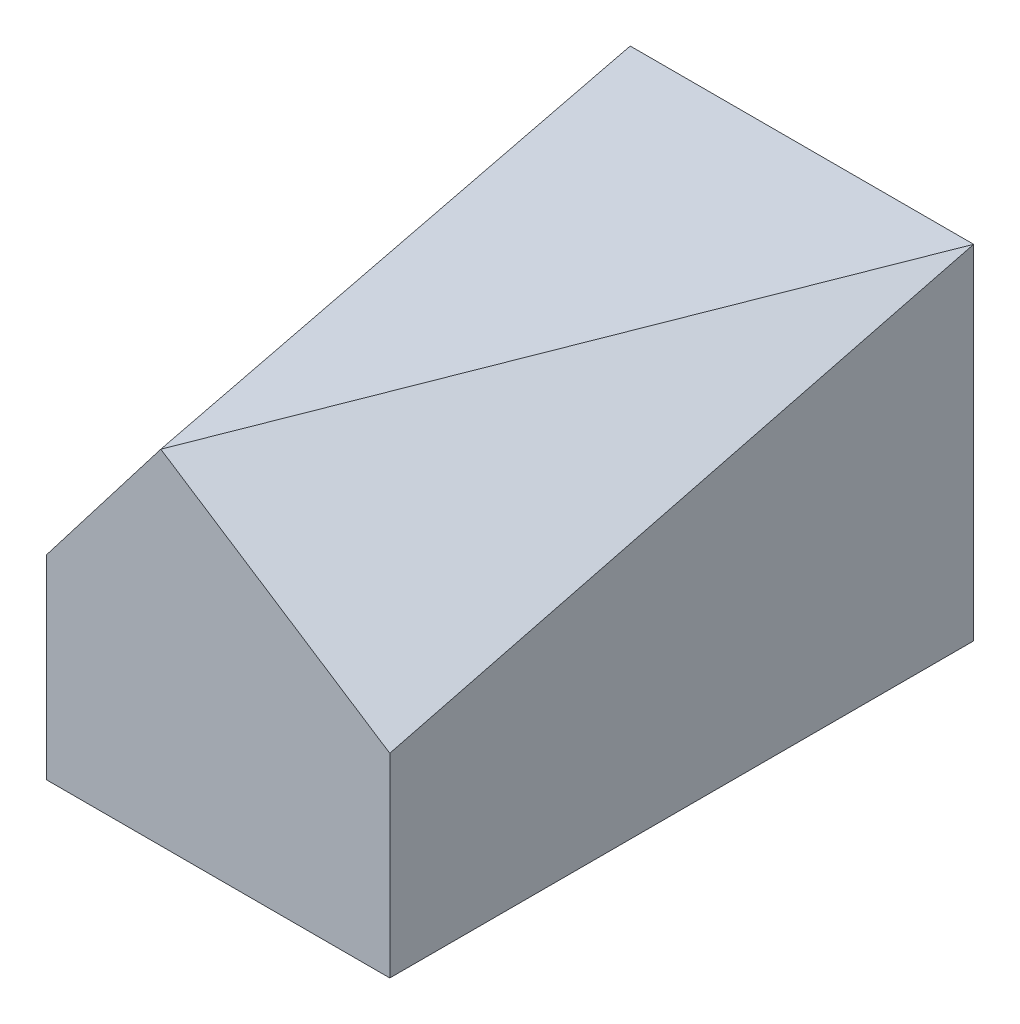
SolidWorks part; units mm, degrees
ref_plane "Front Plane" through (0, 0, 0) normal (0, 0, 1) x (1, 0, 0)
ref_plane "Top Plane" through (0, 0, 0) normal (0, 1, 0) x (1, 0, 0)
ref_plane "Right Plane" through (0, 0, 0) normal (1, 0, 0) x (0, 0, -1)
sketch "Sketch2" plane through (0, 0, 0) normal (0, 1, 0) x (1, 0, 0)
  line L0 (0, 0) -> (0, 51)
  line L1 (0, 51) -> (30, 51)
  line L2 (30, 51) -> (30, 0)
  line L3 (30, 0) -> (0, 0)
  dimension "D1" = 51
  dimension "D2" = 30
extrude "Boss-Extrude1" add sketch "Sketch2" along normal blind 30
sketch "Sketch3" plane through (0, 0, 0) normal (0, 0, 1) x (1, 0, 0)
  line L0 (10, 30) -> (0, 17)
  line L1 (0, 30) -> (30, 30) construction
  line L2 (0, 30) -> (0, 0) construction
  line L3 (10, 30) -> (30, 17)
  line L4 (30, 30) -> (30, 0) construction
  dimension "D1" = 13
  dimension "D2" = 13
  dimension "D3" = 10
ref_plane "Plane1" through (15.9498, 24.5382, 6.2548) normal (0.533, 0.8199, 0.209) x (0.8461, -0.5164, -0.1316)
other "SurfaceCut2"
ref_plane "Plane2" through (-8.0219, 6.1707, 1.5729) normal (0.7832, -0.6025, -0.1536) x (-0.1217, 0.0936, -0.9881)
other "SurfaceCut3"
